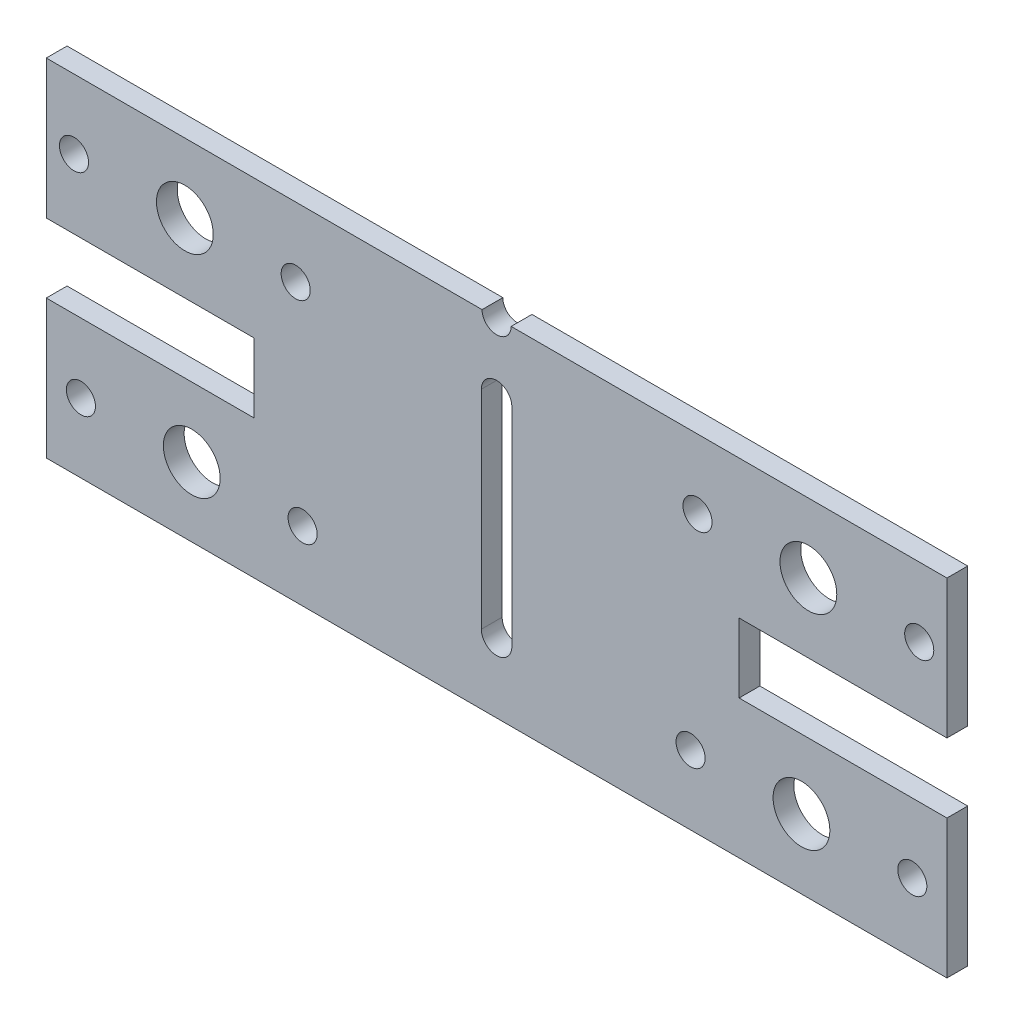
SolidWorks part; units mm, degrees
ref_plane "Plan de face" through (0, 0, 0) normal (0, 0, 1) x (1, 0, 0)
ref_plane "Plan de dessus" through (0, 0, 0) normal (0, 1, 0) x (1, 0, 0)
ref_plane "Plan de droite" through (0, 0, 0) normal (1, 0, 0) x (0, 0, -1)
sketch "Esquisse1" plane through (0, 0, 0) normal (0, 0, 1) x (1, 0, 0)
  line L1 (0, 0) -> (130, 0)
  line L2 (0, 0) -> (0, 50)
  line L3 (0, 50) -> (130, 50)
  line L4 (130, 0) -> (130, 50)
  line L5 (65, 0) -> (65, 10) construction
  line L6 (65, 10) -> (130, 10) construction
  line L7 (130, 40) -> (0, 40) construction
  line L8 (130, 10) -> (0, 10) construction
  line L9 (65, 10) -> (65, 40) construction
  line L10 (0, 40) -> (4, 40) construction
  line L11 (62.8, 10) -> (62.8, 40)
  line L12 (4, 40) -> (20, 40) construction
  line L13 (20, 40) -> (36, 40) construction
  line L14 (130, 40) -> (126, 40) construction
  line L15 (126, 40) -> (110, 40) construction
  line L16 (110, 40) -> (94, 40) construction
  line L17 (0, 10) -> (5, 10) construction
  line L18 (5, 10) -> (21, 10) construction
  line L19 (21, 10) -> (37, 10) construction
  line L20 (130, 10) -> (125, 10) construction
  line L21 (125, 10) -> (109, 10) construction
  line L22 (109, 10) -> (93, 10) construction
  line L23 (67.2, 10) -> (67.2, 40)
  circle A0 centre (4, 40) radius 2.1
  circle A1 centre (20, 40) radius 4.1
  circle A2 centre (36, 40) radius 2.1
  circle A3 centre (94, 40) radius 2.1
  circle A4 centre (110, 40) radius 4.1
  circle A5 centre (126, 40) radius 2.1
  circle A8 centre (5, 10) radius 2.1
  circle A9 centre (21, 10) radius 4.1
  circle A10 centre (37, 10) radius 2.1
  circle A11 centre (93, 10) radius 2.1
  circle A12 centre (109, 10) radius 4.1
  circle A13 centre (125, 10) radius 2.1
  arc A14 (62.8, 10) -> (67.2, 10) centre (65, 10) ccw
  arc A15 (67.2, 40) -> (62.8, 40) centre (65, 40) ccw
  point P5 (65, 43.8114)
  point P6 (65, 50)
  point P16 (65, 25)
  point P38 (65, 10)
  point P45 (65, 26.2368)
  point P46 (0, 0)
  dimension "D18" = 4.2
  dimension "D19" = 4.2
  dimension "D20" = 4.2
  dimension "D21" = 4.2
  dimension "D22" = 4.2
  dimension "D23" = 4.2
  dimension "D24" = 4.2
  dimension "D25" = 4.2
  dimension "D26" = 8.2
  dimension "D27" = 8.2
  dimension "D28" = 8.2
  dimension "D29" = 8.2
  dimension "D30" = 4.4
  dimension "D32" = 10
  dimension "D1" = 130
  dimension "D2" = 50
  dimension "D4" = 10
  dimension "D6" = 4
  dimension "D7" = 16
  dimension "D8" = 16
  dimension "D9" = 4
  dimension "D10" = 16
  dimension "D11" = 16
  dimension "D12" = 5
  dimension "D13" = 16
  dimension "D14" = 16
  dimension "D15" = 5
  dimension "D16" = 16
  dimension "D17" = 16
extrude "Boss.-Extru.1" add sketch "Esquisse1" along normal blind 3
sketch "Esquisse2" plane through (0, 0, 0) normal (0, 0, -1) x (-1, 0, 0)
  line L0 (0, 50) -> (0, 0) construction
  line L1 (0, 20) -> (-30, 20)
  line L2 (0, 20) -> (0, 30)
  line L3 (0, 30) -> (-30, 30)
  line L4 (-30, 20) -> (-30, 30)
  line L5 (-65, 0) -> (-65, 50) construction
  line L6 (0, 0) -> (-130, 0) construction
  line L7 (-130, 50) -> (0, 50) construction
  line L8 (-130, 30) -> (-100, 30)
  line L9 (-100, 20) -> (-100, 30)
  line L10 (-130, 20) -> (-100, 20)
  line L11 (-130, 20) -> (-130, 30)
  line L12 (-62.9, 50) -> (-67.1, 50)
  arc A0 (-67.1, 50) -> (-62.9, 50) centre (-65, 50) ccw
  point P6 (0, 25)
  point P7 (0, 25)
  dimension "D3" = 2.1
  dimension "D1" = 30
  dimension "D2" = 20
extrude "Enlèv. mat.-Extru.1" cut sketch "Esquisse2" against normal up to next
equation "\"D3@Esquisse2\"=4.2/2"
